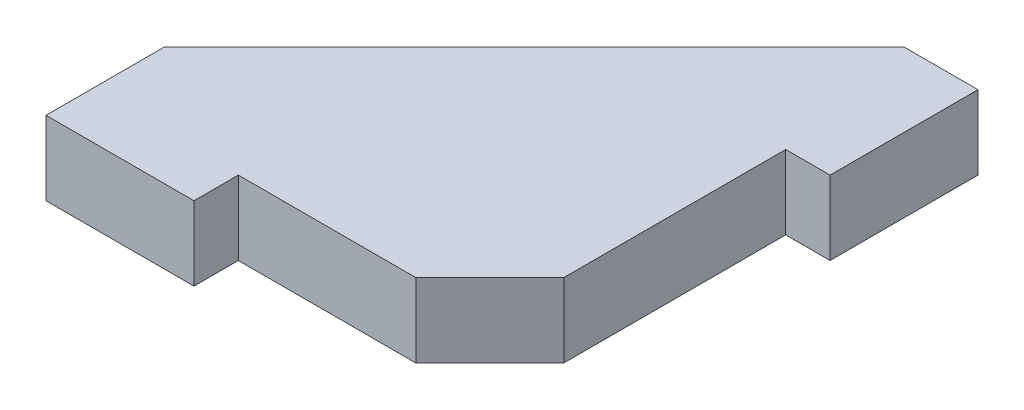
SolidWorks part; units mm, degrees
ref_plane "Front Plane" through (0, 0, 0) normal (0, 0, 1) x (1, 0, 0)
ref_plane "Top Plane" through (0, 0, 0) normal (0, 1, 0) x (1, 0, 0)
ref_plane "Right Plane" through (0, 0, 0) normal (1, 0, 0) x (0, 0, -1)
sketch "Sketch1" plane through (0, 0, 0) normal (0, 1, 0) x (1, 0, 0)
  line L0 (0, 0) -> (0, 8)
  line L1 (0, 8) -> (25, 33)
  line L2 (25, 33) -> (30, 33)
  line L3 (30, 33) -> (30, 23)
  line L4 (30, 23) -> (27, 23)
  line L5 (27, 23) -> (27, 8)
  line L6 (27, 8) -> (22, 3)
  line L7 (22, 3) -> (10, 3)
  line L8 (10, 3) -> (10, 0)
  line L9 (10, 0) -> (0, 0)
  dimension "D1" = 10
  dimension "D2" = 3
  dimension "D3" = 27
  dimension "D4" = 30
  dimension "D5" = 45
  dimension "D6" = 5
  dimension "D7" = 5
extrude "Boss-Extrude1" add sketch "Sketch1" along normal blind 5
